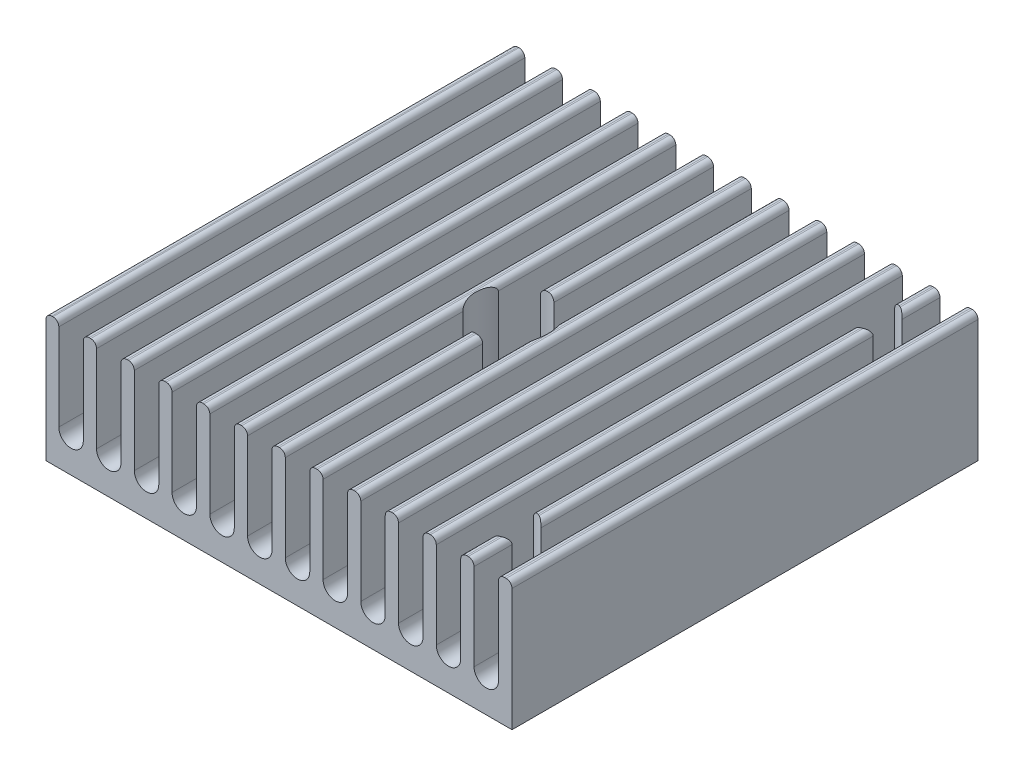
SolidWorks part; units mm, degrees
ref_plane "Спереди" through (0, 0, 0) normal (0, 0, 1) x (1, 0, 0)
ref_plane "Сверху" through (0, 0, 0) normal (0, 1, 0) x (1, 0, 0)
ref_plane "Справа" through (0, 0, 0) normal (1, 0, 0) x (0, 0, -1)
sketch "Эскиз1" plane through (0, 0, 0) normal (0, 0, 1) x (1, 0, 0)
  line L1 (0, 0) -> (40, 0)
  line L2 (0, 0) -> (0, 11)
  line L3 (0, 11) -> (40, 11)
  line L4 (40, 0) -> (40, 11)
  dimension "D1" = 11
  dimension "D2" = 40
extrude "Бобышка-Вытянуть1" add sketch "Эскиз1" along normal blind 40
sketch "Эскиз2" plane through (0, 0, 0) normal (0, 0, -1) x (-1, 0, 0)
  line L0 (-2.15, 3.05) -> (-2.15, 15.2749) construction
  line L1 (-3.2, 3.05) -> (-3.2, 15.2749)
  line L2 (-1.1, 3.05) -> (-1.1, 15.2749)
  line L5 (0, 11) -> (0, 0) construction
  line L6 (0, 0) -> (-40, 0) construction
  arc A0 (-3.2, 3.05) -> (-1.1, 3.05) centre (-2.15, 3.05) ccw
  arc A1 (-1.1, 15.2749) -> (-3.2, 15.2749) centre (-2.15, 15.2749) ccw
  point P2 (-2.15, 9.1625)
  dimension "D1" = 2.1
  dimension "D2" = 1.1
  dimension "D3" = 3.05
extrude "Вырез-Вытянуть1" cut sketch "Эскиз2" against normal blind 40
pattern_linear "Линейный массив1" count 12 spacing 3.24 along (1, 0, 0) of "Вырез-Вытянуть1"
fillet "Скругление1" radius 0.5 2 edges at (1.1, 11, 20) (0, 11, 20)
fillet "Скругление2" radius 0.5 24 edges at (40, 11, 20) (38.84, 11, 20) (36.74, 11, 20) (35.6, 11, 20) (33.5, 11, 20) (32.36, 11, 20) (30.26, 11, 20) (29.12, 11, 20) (27.02, 11, 20) (25.88, 11, 20) (23.78, 11, 20) (22.64, 11, 20) (20.54, 11, 20) (19.4, 11, 20) (17.3, 11, 20) (16.16, 11, 20) (14.06, 11, 20) (12.92, 11, 20) (10.82, 11, 20) (9.68, 11, 20) (7.58, 11, 20) (6.44, 11, 20) (4.34, 11, 20) (3.2, 11, 20)
sketch "Эскиз3" plane through (0, 0, 0) normal (0, -1, 0) x (1, 0, 0)
  line L0 (0, 0) -> (40, 0) construction
  line L1 (40, 40) -> (40, 0) construction
  circle A0 centre (20, 20) radius 3.1
  dimension "D1" = 20
  dimension "D2" = 20
extrude "Вырез-Вытянуть2" cut sketch "Эскиз3" against normal blind 40
sketch "Эскиз4" plane through (0, 0, 0) normal (0, -1, 0) x (1, 0, 0)
  circle A0 centre (35.5, 35.5) radius 1.75
  circle A1 centre (35.5, 4.5) radius 1.75
extrude "Вырез-Вытянуть3" cut sketch "Эскиз4" against normal blind 17
